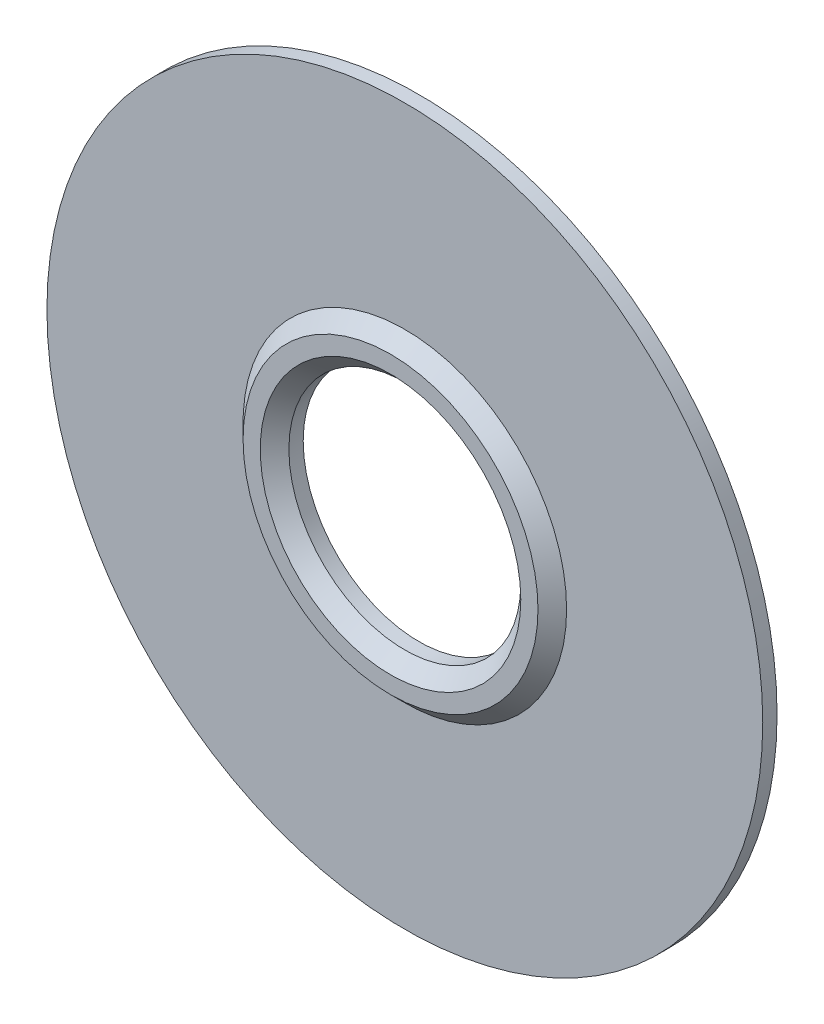
SolidWorks part; units mm, degrees
ref_plane "Płaszczyzna przednia" through (0, 0, 0) normal (0, 0, 1) x (1, 0, 0)
ref_plane "Płaszczyzna górna" through (0, 0, 0) normal (0, 1, 0) x (1, 0, 0)
ref_plane "Płaszczyzna prawa" through (0, 0, 0) normal (1, 0, 0) x (0, 0, -1)
sketch "Szkic1" plane through (0, 0, 0) normal (0, 0, 1) x (1, 0, 0)
  circle A3 centre (-0.0658, 4.9786) radius 25
  circle A4 centre (-0.0658, 4.9786) radius 8 construction
  circle A5 centre (-0.0658, 4.9786) radius 8.1
  dimension "D1" = 0.1
extrude "Dodanie-wyciągnięcie1" add sketch "Szkic1" against normal blind 1 contours A3 A5
sketch "Szkic2" plane through (0, 0, 0) normal (0, 0, 1) x (1, 0, 0)
  circle A0 centre (-0.0658, 4.9786) radius 8.1 construction
  circle A1 centre (-0.0658, 4.9786) radius 8.1
  circle A2 centre (-0.0658, 4.9786) radius 11.1 construction
  circle A3 centre (-0.0658, 4.9786) radius 11.1 construction
  circle A4 centre (-0.0658, 4.9786) radius 11.3
  dimension "D1" = 0.2
extrude "Dodanie-wyciągnięcie2" add sketch "Szkic2" along normal blind 1 draft 45
